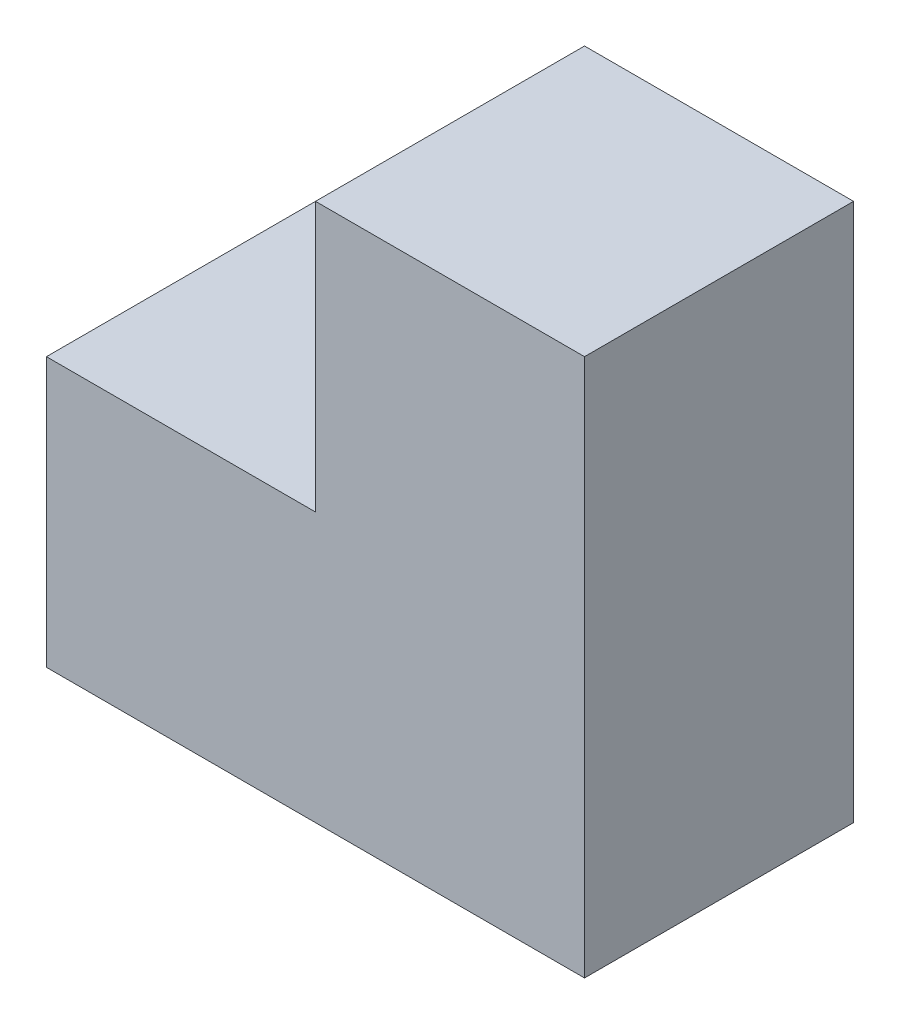
SolidWorks part; units mm, degrees
material "PVC 0.007 Plasticized"
ref_plane "Front Plane" through (0, 0, 0) normal (0, 0, 1) x (1, 0, 0)
ref_plane "Top Plane" through (0, 0, 0) normal (0, 1, 0) x (1, 0, 0)
ref_plane "Right Plane" through (0, 0, 0) normal (1, 0, 0) x (0, 0, -1)
sketch "Sketch1" plane through (0, 0, 0) normal (0, 0, 1) x (1, 0, 0)
  line L0 (0, 0) -> (60, 0)
  line L1 (60, 0) -> (60, 60)
  line L2 (60, 60) -> (30, 60)
  line L3 (30, 60) -> (30, 30)
  line L4 (30, 30) -> (0, 30)
  line L5 (0, 30) -> (0, 0)
  dimension "D1" = 60
  dimension "D2" = 60
  dimension "D3" = 30
  dimension "D4" = 30
extrude "Boss-Extrude1" add sketch "Sketch1" along normal blind 30
